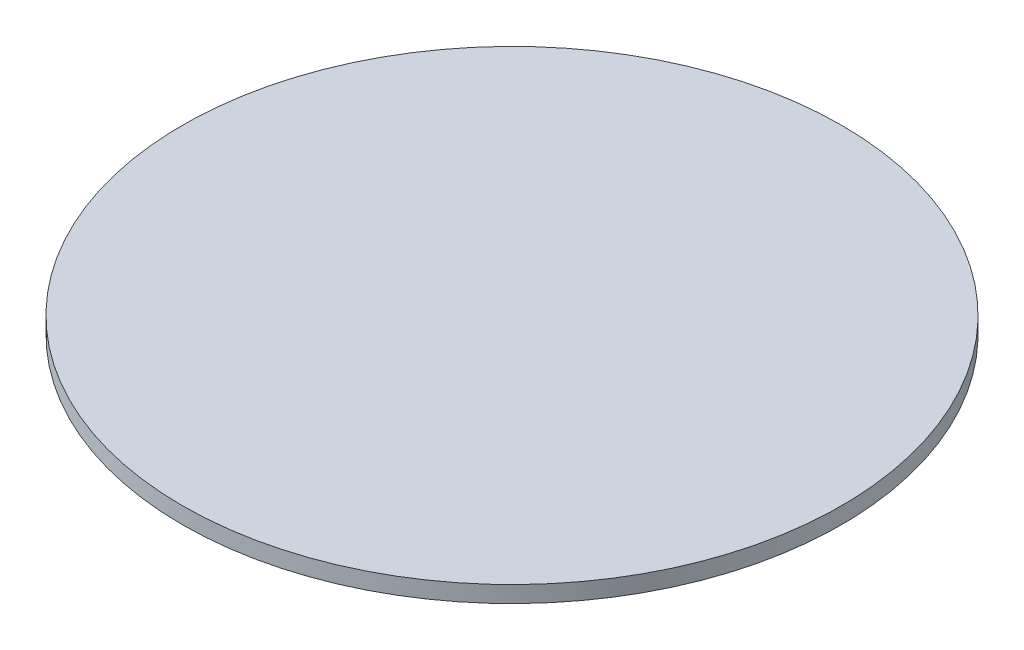
SolidWorks part; units mm, degrees
ref_plane "Front Plane" through (0, 0, 0) normal (0, 0, 1) x (1, 0, 0)
ref_plane "Top Plane" through (0, 0, 0) normal (0, 1, 0) x (1, 0, 0)
ref_plane "Right Plane" through (0, 0, 0) normal (1, 0, 0) x (0, 0, -1)
sketch "Sketch1" plane through (0, 0, 0) normal (0, 1, 0) x (1, 0, 0)
  circle A0 centre (0, 0) radius 10
  dimension "D1" = 20
extrude "PFA film" add sketch "Sketch1" along normal blind 0.5
